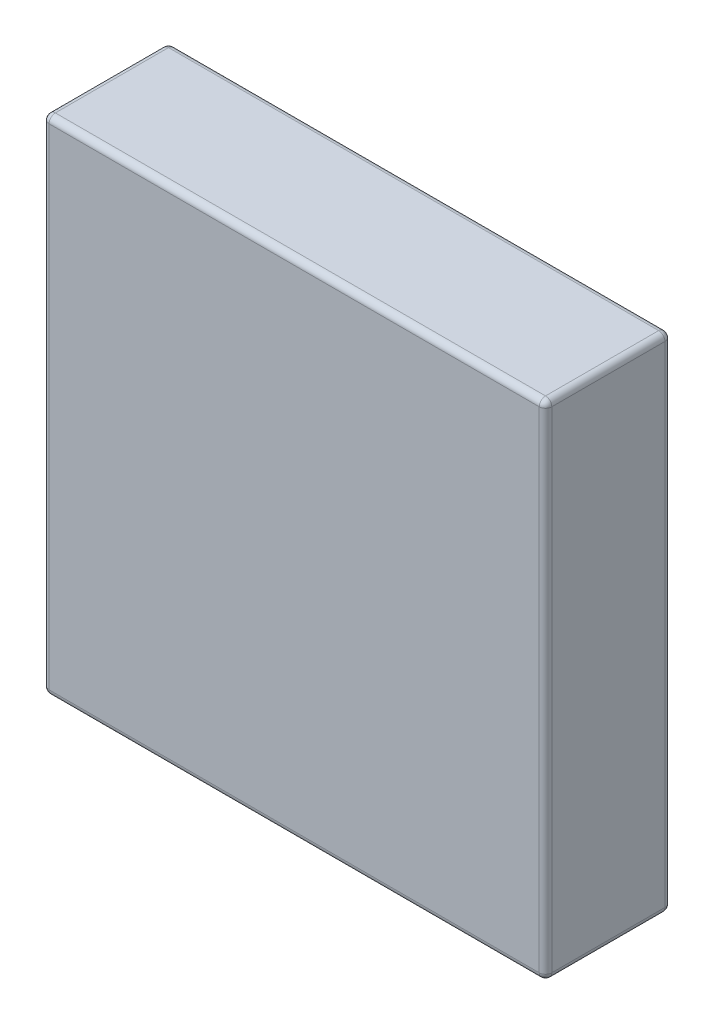
SolidWorks part; units mm, degrees
ref_plane "前视基准面" through (0, 0, 0) normal (0, 0, 1) x (1, 0, 0)
ref_plane "上视基准面" through (0, 0, 0) normal (0, 1, 0) x (1, 0, 0)
ref_plane "右视基准面" through (0, 0, 0) normal (1, 0, 0) x (0, 0, -1)
sketch "草图1" plane through (0, 0, 0) normal (0, 0, 1) x (1, 0, 0)
  line L1 (0, 0) -> (40, 0)
  line L2 (0, 0) -> (0, 40)
  line L3 (0, 40) -> (40, 40)
  line L4 (40, 0) -> (40, 40)
  dimension "D1" = 40
extrude "凸台-拉伸1" add sketch "草图1" along normal blind 10
fillet "圆角1" radius 0.5 12 edges at (0, 0, 5) (20, 0, 10) (0, 20, 10) (20, 0, 0) (0, 20, 0) (40, 0, 5) (40, 20, 10) (40, 20, 0) (40, 40, 5) (20, 40, 10) (0, 40, 5) (20, 40, 0)
